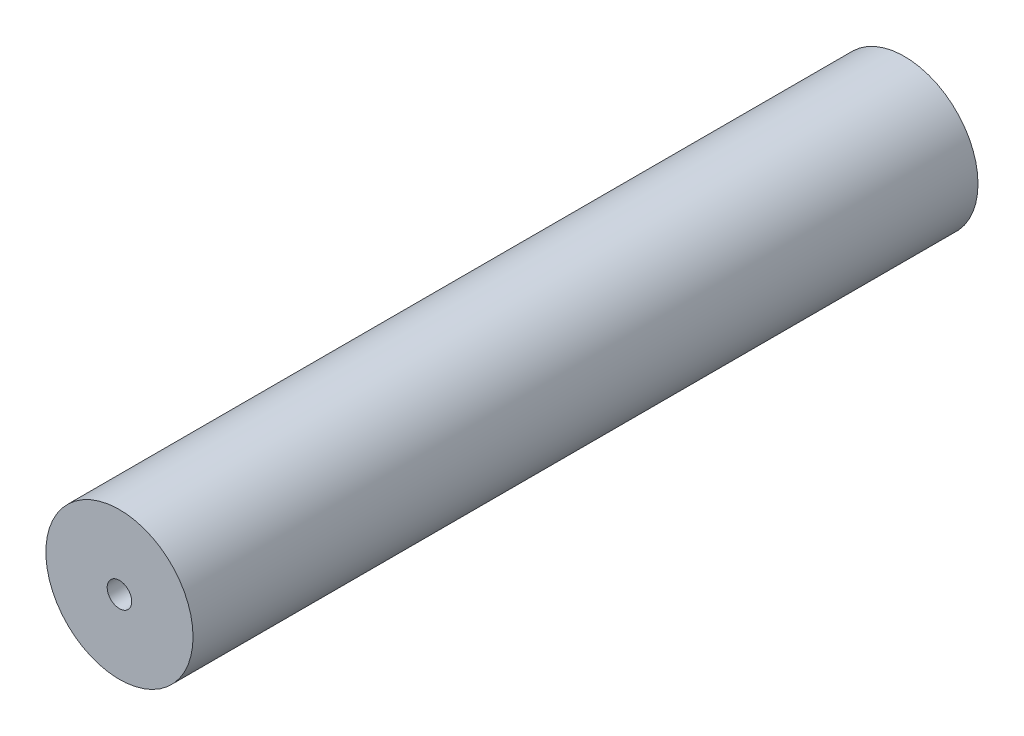
SolidWorks part; units mm, degrees
material "ｱｸﾘﾙ (中-上級の耐衝撃性)"
ref_plane "正面" through (0, 0, 0) normal (0, 0, 1) x (1, 0, 0)
ref_plane "平面" through (0, 0, 0) normal (0, 1, 0) x (1, 0, 0)
ref_plane "右側面" through (0, 0, 0) normal (1, 0, 0) x (0, 0, -1)
sketch "ｽｹｯﾁ1" plane through (0, 0, 0) normal (0, 0, 1) x (1, 0, 0)
  circle A0 centre (0, 0) radius 7.5
  dimension "D1" = 15
extrude "ﾎﾞｽ - 押し出し1" add sketch "ｽｹｯﾁ1" along normal blind 80
hole_wizard "M3x0.5 ねじ穴1" positions "ｽｹｯﾁ4" profile "ｽｹｯﾁ3" tap size "M3x0.5" standard "JIS"
sketch "ｽｹｯﾁ4" plane through (0, 0, 80) normal (0, 0, 1) x (1, 0, 0)
  point P0 (0, 0)
sketch "ｽｹｯﾁ3" plane through (0, 0, 80) normal (1, 0, 0) x (0, -1, 0)
  line L0 (0, 0) -> (0, 10.7511)
  line L1 (0, 10.7511) -> (1.25, 10)
  line L2 (1.25, 10) -> (1.25, 0)
  line L5 (1.25, 0) -> (0, 0)
  line L10 (0, 10.7511) -> (-1.25, 10) construction
  line L11 (0, -6.35) -> (0, 107.95) construction
  dimension "ねじ下穴ﾄﾞﾘﾙ直径" = 2.5
  dimension "ねじ下穴ﾄﾞﾘﾙの深さ" = 10
  dimension "ﾄﾞﾘﾙ角度" = 118
cosmetic thread "穴のねじ山1" parameters "D1"=7, "D2"=3
sketch "ｽｹｯﾁ6" plane through (0, 0, 0) normal (0, 0, -1) x (-1, 0, 0)
  point P0 (0, 0)
hole_wizard "M3x0.5 ねじ穴2" positions "ｽｹｯﾁ8" profile "ｽｹｯﾁ7" tap size "M3x0.5" standard "JIS"
sketch "ｽｹｯﾁ8" plane through (0, 0, 0) normal (0, 0, -1) x (-1, 0, 0)
  point P0 (0, 0)
sketch "ｽｹｯﾁ7" plane through (0, 0, 0) normal (1, 0, 0) x (0, 1, 0)
  line L0 (0, 0) -> (0, 10.7511)
  line L1 (0, 10.7511) -> (1.25, 10)
  line L2 (1.25, 10) -> (1.25, 0)
  line L5 (1.25, 0) -> (0, 0)
  line L10 (0, 10.7511) -> (-1.25, 10) construction
  line L11 (0, -6.35) -> (0, 107.95) construction
  dimension "ねじ下穴ﾄﾞﾘﾙ直径" = 2.5
  dimension "ねじ下穴ﾄﾞﾘﾙの深さ" = 10
  dimension "ﾄﾞﾘﾙ角度" = 118
cosmetic thread "穴のねじ山2" parameters "D1"=7, "D2"=3
